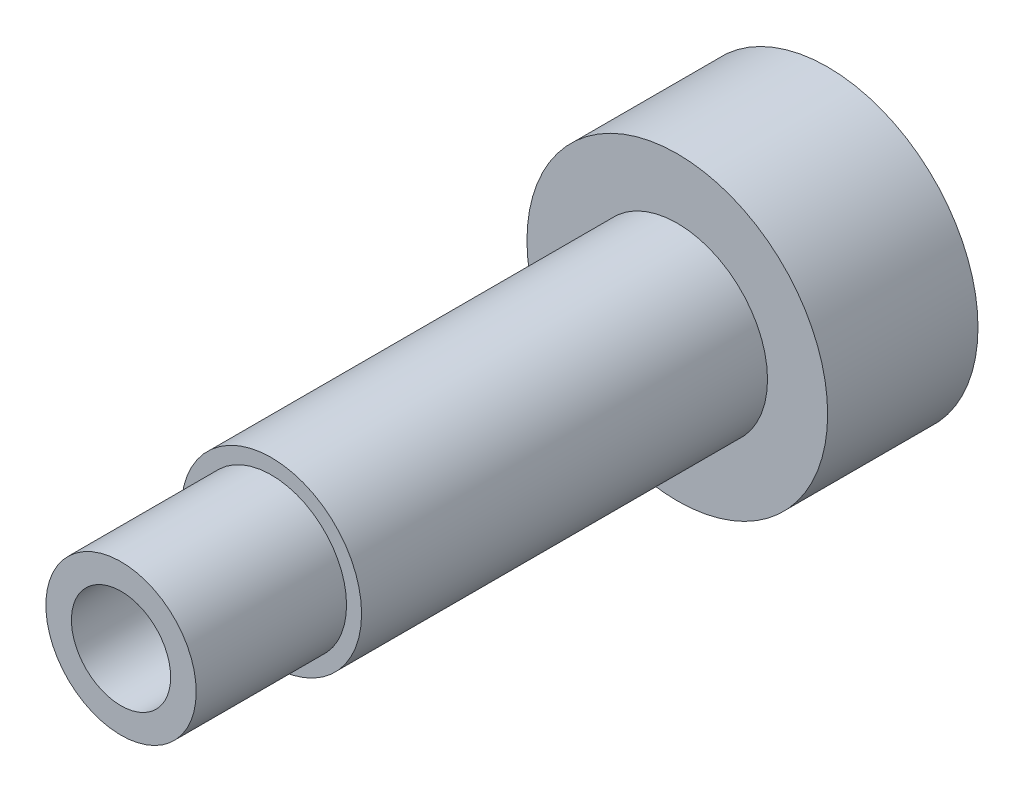
SolidWorks part; units mm, degrees
material "7079 Alloy"
ref_plane "Front Plane" through (0, 0, 0) normal (0, 0, 1) x (1, 0, 0)
ref_plane "Top Plane" through (0, 0, 0) normal (0, 1, 0) x (1, 0, 0)
ref_plane "Right Plane" through (0, 0, 0) normal (1, 0, 0) x (0, 0, -1)
sketch "Sketch1" plane through (0, 0, 0) normal (0, 0, 1) x (1, 0, 0)
  circle A0 centre (0, 0) radius 3
  dimension "D1" = 6
extrude "Extrude1" add sketch "Sketch1" along normal blind 13.5
sketch "Sketch2" plane through (0, 0, 13.5) normal (0, 0, 1) x (1, 0, 0)
  circle A0 centre (0, 0) radius 2.5
  dimension "D1" = 5
extrude "Extrude2" add sketch "Sketch2" along normal blind 5
sketch "Sketch3" plane through (0, 0, 0) normal (0, 0, -1) x (-1, 0, 0)
  circle A0 centre (0, 0) radius 5
  dimension "D1" = 10
extrude "Extrude3" add sketch "Sketch3" along normal blind 5
hole_wizard "M4x0.7 Tapped Hole1" positions "3DSketch1" profile "Sketch4" tap size "M4x0.7" standard "Ansi Metric"
sketch3d "3DSketch1"
  point P3 (0, 0, 18.5)
sketch "Sketch4" plane through (0, 0, 18.5) normal (1, 0, 0) x (0, -1, 0)
  line L0 (0, 0) -> (0, 11.0914)
  line L1 (0, 11.0914) -> (1.65, 10.1)
  line L2 (1.65, 10.1) -> (1.65, 0)
  line L5 (1.65, 0) -> (0, 0)
  line L10 (0, 11.0914) -> (-1.65, 10.1) construction
  line L11 (0, -6.35) -> (0, 107.95) construction
  dimension "Tap Drill Dia." = 3.3
  dimension "Tap Drill Depth" = 10.1
  dimension "Drill Angle" = 118
cosmetic thread "Hole Thread1" parameters "D1"=8, "D2"=4
